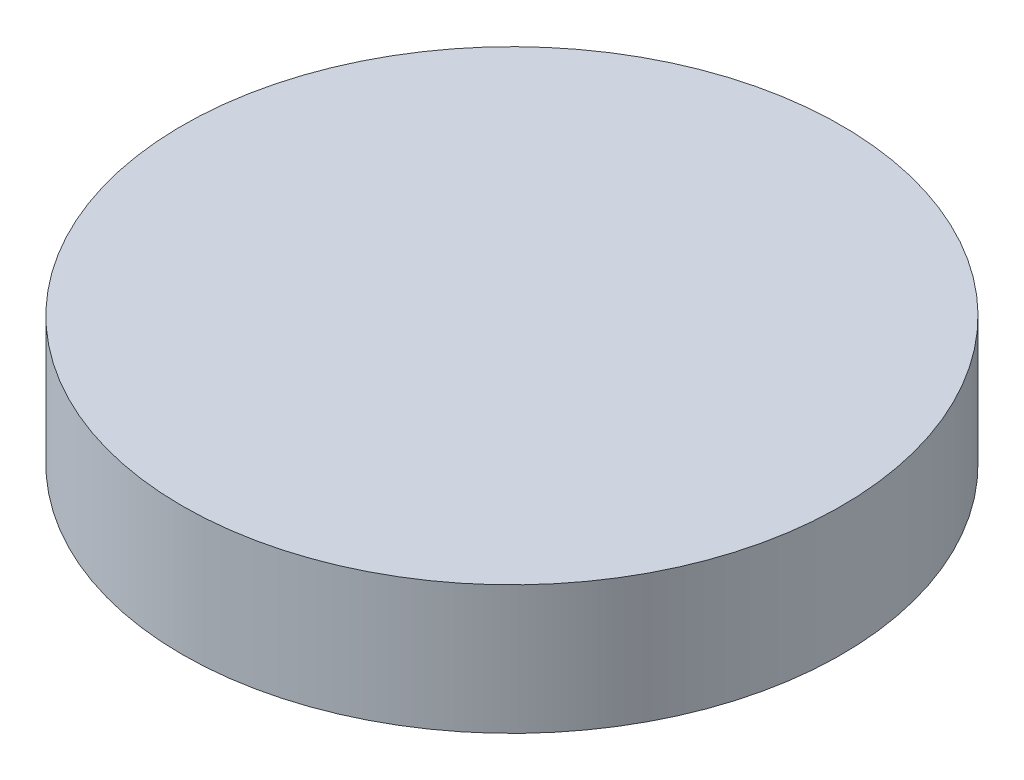
SolidWorks part; units mm, degrees
ref_plane "前视基准面" through (0, 0, 0) normal (0, 0, 1) x (1, 0, 0)
ref_plane "上视基准面" through (0, 0, 0) normal (0, 1, 0) x (1, 0, 0)
ref_plane "右视基准面" through (0, 0, 0) normal (1, 0, 0) x (0, 0, -1)
sketch "草图1" plane through (0, 0, 0) normal (0, 1, 0) x (1, 0, 0)
  circle A0 centre (0, 0) radius 6.25
  dimension "D1" = 12.5
extrude "凸台-拉伸1" add sketch "草图1" along normal blind 2.44
